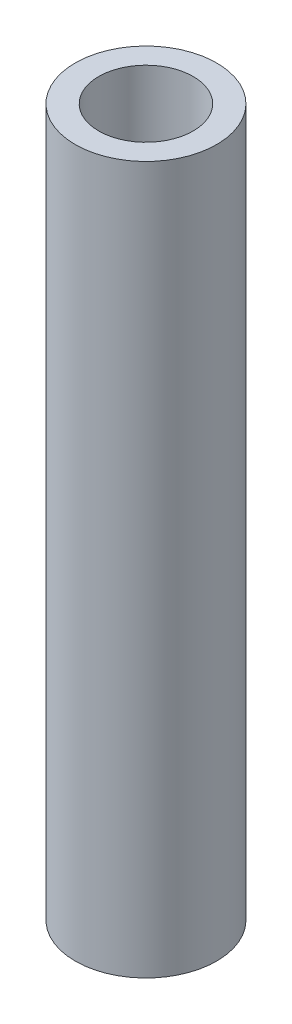
SolidWorks part; units mm, degrees
ref_plane "Front Plane" through (0, 0, 0) normal (0, 0, 1) x (1, 0, 0)
ref_plane "Top Plane" through (0, 0, 0) normal (0, 1, 0) x (1, 0, 0)
ref_plane "Right Plane" through (0, 0, 0) normal (1, 0, 0) x (0, 0, -1)
sketch "Sketch1" plane through (0, 0, 0) normal (0, 1, 0) x (1, 0, 0)
  circle A0 centre (0, 0) radius 25
  circle A1 centre (0, 0) radius 16.7
  dimension "D1" = 50
  dimension "D2" = 8.3
extrude "Boss-Extrude1" add sketch "Sketch1" along normal mid plane 250
